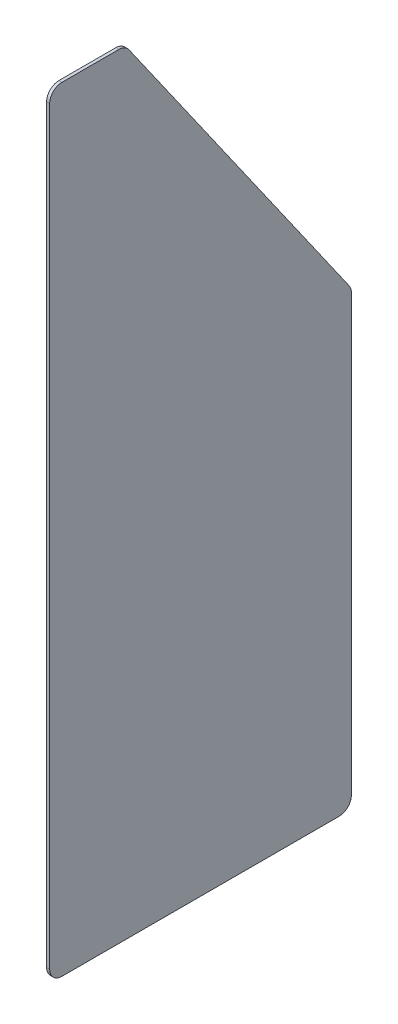
SolidWorks part; units mm, degrees
material "PC High Viscosity"
ref_plane "Front Plane" through (0, 0, 0) normal (0, 0, 1) x (1, 0, 0)
ref_plane "Top Plane" through (0, 0, 0) normal (0, 1, 0) x (1, 0, 0)
ref_plane "Right Plane" through (0, 0, 0) normal (1, 0, 0) x (0, 0, -1)
sketch "Sketch1" plane through (0, 0, 0) normal (0, 1, 0) x (1, 0, 0)
  line L4 (1.5875, 155.8925) -> (0, 155.8925)
  line L5 (0, 155.8925) -> (0, 0)
  line L6 (1.5875, 155.8925) -> (1.5875, 0)
  line L7 (1.5875, 0) -> (0, 0)
  dimension "D1" = 155.8925
  dimension "D4" = 1.5875
extrude "Boss-Extrude1" add sketch "Sketch1" along normal blind 400.05
sketch "Sketch2" plane through (0, 0, 0) normal (-1, 0, 0) x (0, 0, 1)
  line L0 (-39.0433, 400.05) -> (-155.8925, 233.172)
  line L1 (-155.8925, 233.172) -> (-155.8925, 400.05)
  line L2 (-155.8925, 400.05) -> (-39.0433, 400.05)
  line L3 (-155.8925, 400.05) -> (-155.8925, 0) construction
  line L4 (-155.8925, 400.05) -> (0, 400.05) construction
  point P12 (-156.9204, 391.3772)
  dimension "D1" = 166.878
  dimension "D2" = 55
extrude "Cut-Extrude1" cut sketch "Sketch2" against normal up to surface (1.5875 mm away) up to face at (1.5875, 200.025, -77.9462)
fillet "Fillet1" radius 6.35 5 edges at (0.7937, 0, -155.8925) (0.7938, 0, 0) (0.7938, 400.05, 0) (0.7937, 400.05, -39.0433) (0.7938, 233.172, -155.8925)
